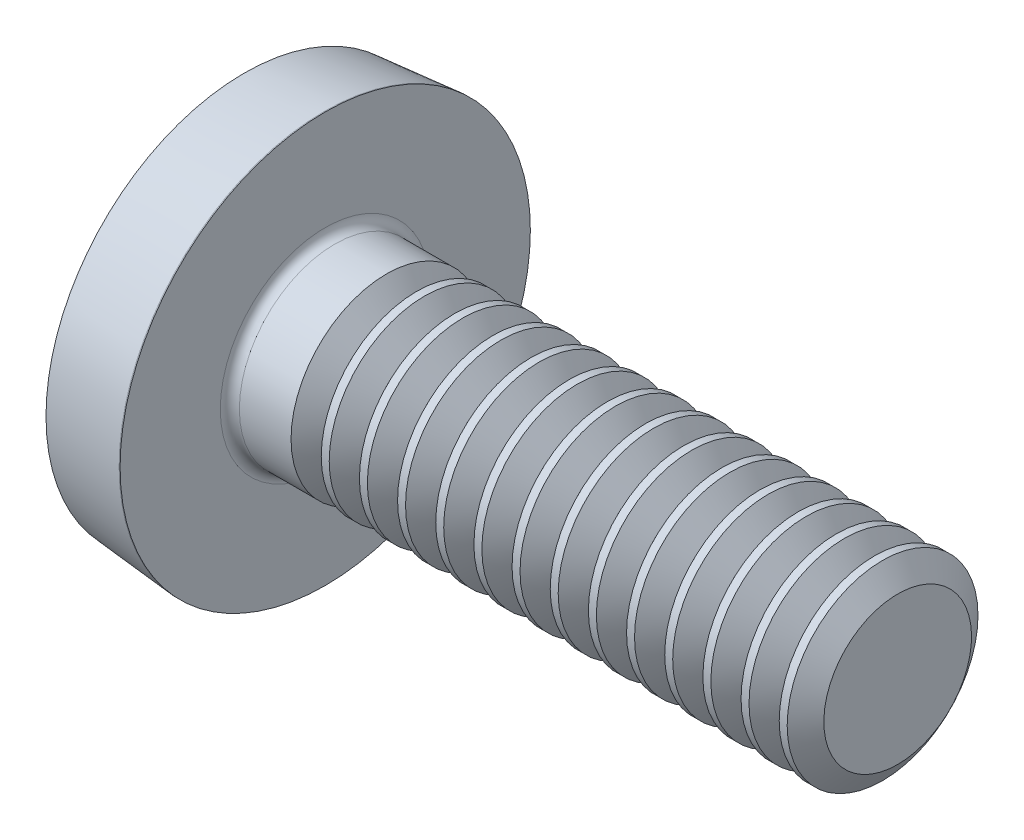
SolidWorks part; units mm, degrees
ref_plane "Plane1" through (0, 0, 0) normal (0, 0, 1) x (1, 0, 0)
ref_plane "Plane2" through (0, 0, 0) normal (0, 1, 0) x (1, 0, 0)
ref_plane "Plane3" through (0, 0, 0) normal (1, 0, 0) x (0, 0, -1)
sketch "BodySke" plane through (0, 0, 0) normal (0, 0, 1) x (1, 0, 0)
  line L0 (1.2, 1) -> (1.2, 2.15)
  line L1 (1.6, 6.35) -> (1.6, -3.175) construction
  line L2 (-25.4, 0) -> (127, 0) construction
  line L3 (7.2, 0) -> (0, 0)
  line L4 (1.2, 1) -> (7.2, 1)
  line L5 (7.2, 1) -> (7.2, 0)
  line L6 (0.35, 2.0765) -> (1.19, 2.15)
  line L8 (1.2, 6.35) -> (1.2, -3.175) construction
  line L9 (1.2, 2.15) -> (1.19, 2.15)
  arc A0 (0.35, 2.0765) -> (0, 0) centre (6.3348, 0) ccw
  dimension "Length" = 6
  dimension "Head_ht" = 1.2
  dimension "Advance" = 0.4
  dimension "Thread_nom" = 6
  dimension "Diameter" = 2
  dimension "Head_dia" = 4.3
  dimension "Head_ang" = 85
  dimension "Oval_ht" = 0.35
  dimension "D1" = 0.01
revolve "Base-Revolve" add sketch "BodySke"
cosmetic thread "ThreadCosmetic" [suppressed]
fillet "Fillet1" radius 0.1 1 edges at (1.2, 0, 1)
sketch "Sketch3" plane through (0, 0, 0) normal (1, 0, 0) x (0, 0, -1)
  line L0 (0.37, -1.1) -> (-0.37, -1.1)
  line L1 (0.37, -1.1) -> (0.37, 1.1)
  line L2 (-0.37, 1.1) -> (0.37, 1.1)
  line L3 (-0.37, 1.1) -> (-0.37, -1.1)
  dimension "Cross_dia" = 2.2
  dimension "D1" = 1.1
  dimension "Cross_width" = 0.74
  dimension "D2" = 0.37
ref_plane "Plane4" through (1.01, 0, 0) normal (1, 0, 0) x (0, 0, -1)
sketch "Sketch4" plane through (1.01, 0, 0) normal (1, 0, 0) x (0, 0, -1)
  line L0 (0.37, -0.5964) -> (-0.37, -0.5964)
  line L1 (0.37, -0.5964) -> (0.37, 0.5964)
  line L2 (-0.37, 0.5964) -> (0.37, 0.5964)
  line L3 (-0.37, 0.5964) -> (-0.37, -0.5964)
  dimension "D1" = 0.74
  dimension "D2" = 1.1929
  dimension "D3" = 0.37
  dimension "D4" = 0.5964
loft "Recess" cut profiles "Sketch3", "Sketch4"
pattern_circular "RecPat" count 2 every 90 about axis through (0, 0, 0) along (1, 0, 0) of "Recess"
sketch "RecCorSke" plane through (0, 0, 0) normal (0, 0, 1) x (1, 0, 0)
  line L0 (-3.175, 0) -> (15.875, 0) construction
  line L1 (-25.4, 0) -> (127, 0) construction
  line L2 (0, 0) -> (0, 0.6266)
  line L3 (0, 0.6266) -> (1.01, 0.556)
  line L4 (1.01, 0.556) -> (1.1907, 0)
  line L5 (1.1907, 0) -> (0, 0)
  dimension "Diameter" = 1.112
  dimension "Depth" = 1.01
  dimension "Draft_angle" = 4
  dimension "Bottom_angle" = 18
revolve "RecessCore" cut sketch "RecCorSke" angle 360 about L0
sketch "ThdSchSke" plane through (0, 0, 0) normal (0, 0, 1) x (1, 0, 0)
  line L0 (2, -0.774) -> (1.8418, -1)
  line L1 (2, -0.774) -> (2.1582, -1)
  line L2 (2.1582, -1) -> (2.1582, -1.25)
  line L3 (-3.175, 0) -> (5.1513, 0) construction
  line L5 (2.1582, -1.25) -> (1.8418, -1.25)
  line L6 (1.8418, -1.25) -> (1.8418, -1)
  dimension "Diameter" = 2
  dimension "SideAngle" = 55
  dimension "VeeAngle" = 70
  dimension "Thread_minor" = 1.548
  dimension "Overcut" = 2.5
  dimension "Start" = 2
revolve "ThreadSchematic" cut sketch "ThdSchSke" angle 360 about L3
pattern_linear "ThdSchPat" count 14 spacing 0.4 along (1, 0, 0) of "ThreadSchematic"
equation "\"D1@Sketch3\" = \"Cross_dia@Sketch3\" / 2"
equation "\"D2@Sketch3\" = \"Cross_width@Sketch3\" / 2"
equation "\"Depth@RecCorSke\" = \"Cross_depth@Plane4\""
equation "\"D1@Sketch4\" = \"Cross_width@Sketch3\""
equation "\"D2@Sketch4\" = \"Cross_dia@Sketch3\" - 2.0 * \"Cross_depth@Plane4\" * tan(26.5  * 0.017453292)"
equation "\"D3@Sketch4\" = \"D1@Sketch4\" / 2"
equation "\"D4@Sketch4\" = \"D2@Sketch4\" / 2"
equation "\"Thread_length@ThreadCosmetic\" = ((sgn( (\"Length@BodySke\" - \"Advance@BodySke\" * 2.0 ) - \"Thread_nom@BodySke\" )-1)*( (\"Length@BodySke\" - \"Advance@BodySke\" * 2.0 ) - \"Thread_nom@BodySke\" ))/-2+ \"Thread_nom@BodySke\""
equation "\"Thread_minor@ThdSchSke\" = \"Thread_minor@ThreadCosmetic\""
equation "\"Diameter@ThdSchSke\" = \"Diameter@BodySke\""
equation "\"Overcut@ThdSchSke\" = \"Diameter@BodySke\" * 1.25"
equation "\"Start@ThdSchSke\" = \"Head_ht@BodySke\" + \"Length@BodySke\" - \"Thread_length@ThreadCosmetic\"  '---Non-countersunk---"
equation "\"Num_threads@ThdSchPat\" = int( \"Thread_length@ThreadCosmetic\" / \"Advance@BodySke\" + 0.999 )  + 1"
equation "\"Advance@ThdSchPat\" = \"Thread_length@ThreadCosmetic\" /  (\"Num_threads@ThdSchPat\" - 1) 'relax it"
